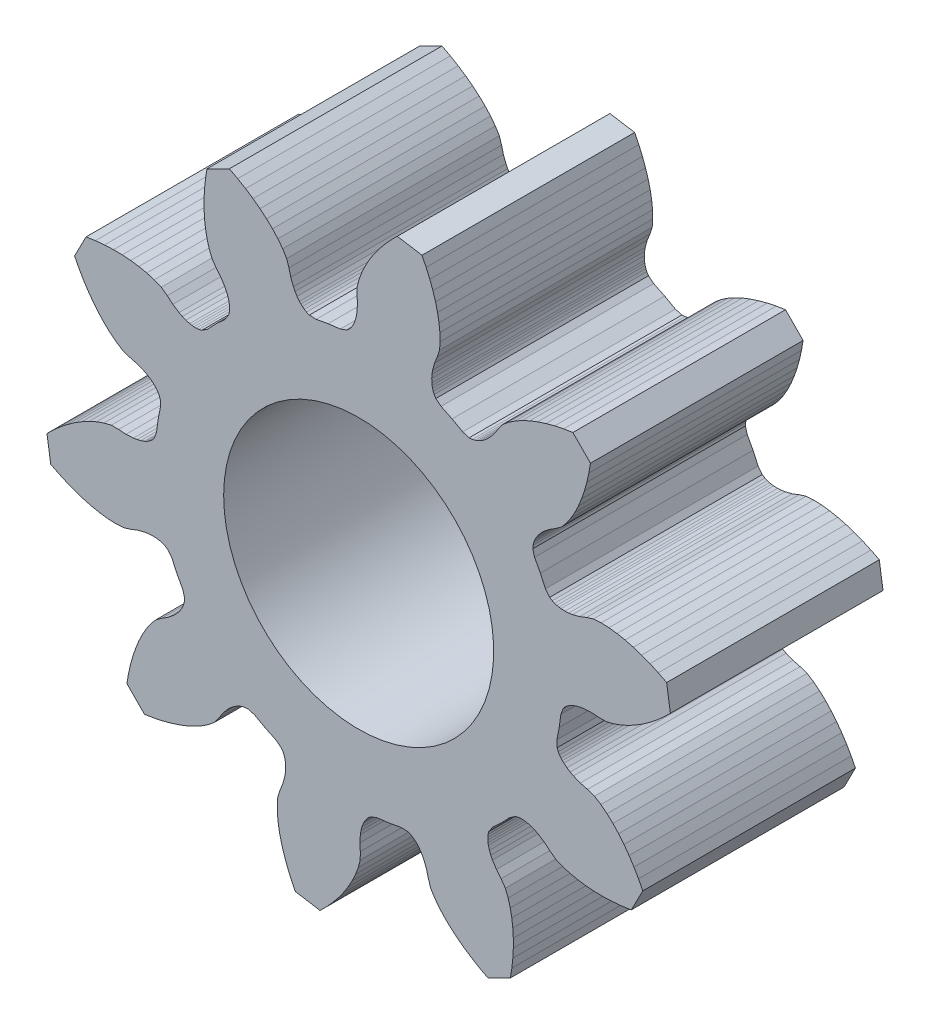
SolidWorks part; units mm, degrees
material "1060 Alloy"
ref_plane "Front Plane" through (0, 0, 0) normal (0, 0, 1) x (1, 0, 0)
ref_plane "Top Plane" through (0, 0, 0) normal (0, 1, 0) x (1, 0, 0)
ref_plane "Right Plane" through (0, 0, 0) normal (1, 0, 0) x (0, 0, -1)
sketch "Sketch1" plane through (0, 0, 0) normal (0, 0, 1) x (1, 0, 0)
  line L0 (-8.7858, -3.765) -> (-8.9815, -3.5156)
  line L1 (-8.9815, -3.5156) -> (-9.1044, -3.4371)
  line L2 (-9.1044, -3.4371) -> (-9.2148, -3.3885)
  line L3 (-9.2148, -3.3885) -> (-9.3186, -3.3562)
  line L4 (-9.3186, -3.3562) -> (-9.4181, -3.3349)
  line L5 (-9.4181, -3.3349) -> (-9.5145, -3.3217)
  line L6 (-9.5145, -3.3217) -> (-9.7003, -3.3138)
  line L7 (-9.7003, -3.3138) -> (-9.8793, -3.3247)
  line L8 (-9.8793, -3.3247) -> (-10.0533, -3.3502)
  line L9 (-10.0533, -3.3502) -> (-10.3894, -3.4364)
  line L10 (-10.3894, -3.4364) -> (-10.7128, -3.5607)
  line L11 (-10.7128, -3.5607) -> (-11.0431, -3.6644)
  line L12 (-11.0431, -3.6644) -> (-11.4, -3.6866)
  line L13 (-11.4, -3.6866) -> (-11.7679, -3.6716)
  line L14 (-11.7679, -3.6716) -> (-12.1438, -3.6256)
  line L15 (-12.1438, -3.6256) -> (-12.5259, -3.5514)
  line L16 (-12.5259, -3.5514) -> (-12.9126, -3.4504)
  line L17 (-12.9126, -3.4504) -> (-13.3028, -3.3238)
  line L18 (-13.3028, -3.3238) -> (-13.6953, -3.1723)
  line L19 (-13.6953, -3.1723) -> (-14.0889, -2.9962)
  line L20 (-14.0889, -2.9962) -> (-14.4827, -2.7961)
  line L21 (-14.4827, -2.7961) -> (-14.6595, -1.6321)
  line L22 (-14.6595, -1.6321) -> (-14.343, -1.324)
  line L23 (-14.343, -1.324) -> (-14.0194, -1.039)
  line L24 (-14.0194, -1.039) -> (-13.6897, -0.7777)
  line L25 (-13.6897, -0.7777) -> (-13.3547, -0.5409)
  line L26 (-13.3547, -0.5409) -> (-13.0154, -0.3297)
  line L27 (-13.0154, -0.3297) -> (-12.6726, -0.1453)
  line L28 (-12.6726, -0.1453) -> (-12.3273, 0.0103)
  line L29 (-12.3273, 0.0103) -> (-11.9805, 0.1339)
  line L30 (-11.9805, 0.1339) -> (-11.6331, 0.2187)
  line L31 (-11.6331, 0.2187) -> (-11.2869, 0.2178)
  line L32 (-11.2869, 0.2178) -> (-10.9412, 0.1951)
  line L33 (-10.9412, 0.1951) -> (-10.5947, 0.2127)
  line L34 (-10.5947, 0.2127) -> (-10.421, 0.24)
  line L35 (-10.421, 0.24) -> (-10.2468, 0.2828)
  line L36 (-10.2468, 0.2828) -> (-10.0717, 0.3455)
  line L37 (-10.0717, 0.3455) -> (-9.9836, 0.3867)
  line L38 (-9.9836, 0.3867) -> (-9.895, 0.4366)
  line L39 (-9.895, 0.4366) -> (-9.8054, 0.4983)
  line L40 (-9.8054, 0.4983) -> (-9.7144, 0.5775)
  line L41 (-9.7144, 0.5775) -> (-9.6204, 0.689)
  line L42 (-9.6204, 0.689) -> (-9.5076, 0.9853)
  line L43 (-9.5076, 0.9853) -> (-9.4312, 1.5547)
  line L44 (-9.4312, 1.5547) -> (-9.3208, 2.1184)
  line L45 (-9.3208, 2.1184) -> (-9.3325, 2.4352)
  line L46 (-9.3325, 2.4352) -> (-9.3858, 2.571)
  line L47 (-9.3858, 2.571) -> (-9.4466, 2.6752)
  line L48 (-9.4466, 2.6752) -> (-9.5116, 2.7624)
  line L49 (-9.5116, 2.7624) -> (-9.5796, 2.8381)
  line L50 (-9.5796, 2.8381) -> (-9.6498, 2.9054)
  line L51 (-9.6498, 2.9054) -> (-9.7955, 3.021)
  line L52 (-9.7955, 3.021) -> (-9.9467, 3.1175)
  line L53 (-9.9467, 3.1175) -> (-10.1024, 3.199)
  line L54 (-10.1024, 3.199) -> (-10.425, 3.3269)
  line L55 (-10.425, 3.3269) -> (-10.7597, 3.4164)
  line L56 (-10.7597, 3.4164) -> (-11.0878, 3.5266)
  line L57 (-11.0878, 3.5266) -> (-11.3896, 3.7184)
  line L58 (-11.3896, 3.7184) -> (-11.6785, 3.9468)
  line L59 (-11.6785, 3.9468) -> (-11.9556, 4.205)
  line L60 (-11.9556, 4.205) -> (-12.221, 4.4896)
  line L61 (-12.221, 4.4896) -> (-12.4746, 4.7986)
  line L62 (-12.4746, 4.7986) -> (-12.7159, 5.1304)
  line L63 (-12.7159, 5.1304) -> (-12.9443, 5.4837)
  line L64 (-12.9443, 5.4837) -> (-13.1593, 5.8575)
  line L65 (-13.1593, 5.8575) -> (-13.3602, 6.2508)
  line L66 (-13.3602, 6.2508) -> (-12.8191, 7.2965)
  line L67 (-12.8191, 7.2965) -> (-12.3819, 7.3597)
  line L68 (-12.3819, 7.3597) -> (-11.9526, 7.4001)
  line L69 (-11.9526, 7.4001) -> (-11.5323, 7.4176)
  line L70 (-11.5323, 7.4176) -> (-11.1221, 7.4123)
  line L71 (-11.1221, 7.4123) -> (-10.7234, 7.3838)
  line L72 (-10.7234, 7.3838) -> (-10.3377, 7.3315)
  line L73 (-10.3377, 7.3315) -> (-9.9669, 7.2544)
  line L74 (-9.9669, 7.2544) -> (-9.6137, 7.1505)
  line L75 (-9.6137, 7.1505) -> (-9.2828, 7.0149)
  line L76 (-9.2828, 7.0149) -> (-9.0033, 6.8107)
  line L77 (-9.0033, 6.8107) -> (-8.7368, 6.5892)
  line L78 (-8.7368, 6.5892) -> (-8.4462, 6.3997)
  line L79 (-8.4462, 6.3997) -> (-8.2897, 6.3197)
  line L80 (-8.2897, 6.3197) -> (-8.1236, 6.2519)
  line L81 (-8.1236, 6.2519) -> (-7.945, 6.1998)
  line L82 (-7.945, 6.1998) -> (-7.8496, 6.1813)
  line L83 (-7.8496, 6.1813) -> (-7.7485, 6.1696)
  line L84 (-7.7485, 6.1696) -> (-7.6398, 6.1668)
  line L85 (-7.6398, 6.1668) -> (-7.5196, 6.1774)
  line L86 (-7.5196, 6.1774) -> (-7.378, 6.2124)
  line L87 (-7.378, 6.2124) -> (-7.1126, 6.3858)
  line L88 (-7.1126, 6.3858) -> (-6.7162, 6.8015)
  line L89 (-6.7162, 6.8015) -> (-6.2955, 7.1927)
  line L90 (-6.2955, 7.1927) -> (-6.1188, 7.4559)
  line L91 (-6.1188, 7.4559) -> (-6.082, 7.597)
  line L92 (-6.082, 7.597) -> (-6.07, 7.7171)
  line L93 (-6.07, 7.7171) -> (-6.0713, 7.8258)
  line L94 (-6.0713, 7.8258) -> (-6.0818, 7.927)
  line L95 (-6.0818, 7.927) -> (-6.099, 8.0227)
  line L96 (-6.099, 8.0227) -> (-6.1489, 8.2019)
  line L97 (-6.1489, 8.2019) -> (-6.2146, 8.3688)
  line L98 (-6.2146, 8.3688) -> (-6.2927, 8.5263)
  line L99 (-6.2927, 8.5263) -> (-6.4784, 8.8194)
  line L100 (-6.4784, 8.8194) -> (-6.6966, 9.0885)
  line L101 (-6.6966, 9.0885) -> (-6.8973, 9.3706)
  line L102 (-6.8973, 9.3706) -> (-7.0287, 9.7032)
  line L103 (-7.0287, 9.7032) -> (-7.1282, 10.0577)
  line L104 (-7.1282, 10.0577) -> (-7.2006, 10.4294)
  line L105 (-7.2006, 10.4294) -> (-7.248, 10.8157)
  line L106 (-7.248, 10.8157) -> (-7.2715, 11.2148)
  line L107 (-7.2715, 11.2148) -> (-7.2717, 11.625)
  line L108 (-7.2717, 11.625) -> (-7.2489, 12.0451)
  line L109 (-7.2489, 12.0451) -> (-7.2031, 12.4739)
  line L110 (-7.2031, 12.4739) -> (-7.1344, 12.9102)
  line L111 (-7.1344, 12.9102) -> (-6.0821, 13.4381)
  line L112 (-6.0821, 13.4381) -> (-5.6913, 13.2322)
  line L113 (-5.6913, 13.2322) -> (-5.3202, 13.0126)
  line L114 (-5.3202, 13.0126) -> (-4.9698, 12.7797)
  line L115 (-4.9698, 12.7797) -> (-4.6411, 12.5343)
  line L116 (-4.6411, 12.5343) -> (-4.3353, 12.2769)
  line L117 (-4.3353, 12.2769) -> (-4.054, 12.0079)
  line L118 (-4.054, 12.0079) -> (-3.7993, 11.7276)
  line L119 (-3.7993, 11.7276) -> (-3.5746, 11.4359)
  line L120 (-3.5746, 11.4359) -> (-3.3866, 11.1317)
  line L121 (-3.3866, 11.1317) -> (-3.2805, 10.8022)
  line L122 (-3.2805, 10.8022) -> (-3.1952, 10.4664)
  line L123 (-3.1952, 10.4664) -> (-3.0714, 10.1422)
  line L124 (-3.0714, 10.1422) -> (-2.9918, 9.9855)
  line L125 (-2.9918, 9.9855) -> (-2.8973, 9.833)
  line L126 (-2.8973, 9.833) -> (-2.7835, 9.6859)
  line L127 (-2.7835, 9.6859) -> (-2.7171, 9.6149)
  line L128 (-2.7171, 9.6149) -> (-2.6422, 9.546)
  line L129 (-2.6422, 9.546) -> (-2.5559, 9.4799)
  line L130 (-2.5559, 9.4799) -> (-2.4524, 9.4178)
  line L131 (-2.4524, 9.4178) -> (-2.3173, 9.3628)
  line L132 (-2.3173, 9.3628) -> (-2.0007, 9.3471)
  line L133 (-2.0007, 9.3471) -> (-1.4356, 9.4504)
  line L134 (-1.4356, 9.4504) -> (-0.8654, 9.5196)
  line L135 (-0.8654, 9.5196) -> (-0.5677, 9.6287)
  line L136 (-0.5677, 9.6287) -> (-0.455, 9.7213)
  line L137 (-0.455, 9.7213) -> (-0.3747, 9.8113)
  line L138 (-0.3747, 9.8113) -> (-0.3119, 9.9001)
  line L139 (-0.3119, 9.9001) -> (-0.2608, 9.9881)
  line L140 (-0.2608, 9.9881) -> (-0.2185, 10.0757)
  line L141 (-0.2185, 10.0757) -> (-0.1536, 10.2499)
  line L142 (-0.1536, 10.2499) -> (-0.1086, 10.4236)
  line L143 (-0.1086, 10.4236) -> (-0.0792, 10.5969)
  line L144 (-0.0792, 10.5969) -> (-0.0572, 10.9432)
  line L145 (-0.0572, 10.9432) -> (-0.0755, 11.2892)
  line L146 (-0.0755, 11.2892) -> (-0.0721, 11.6353)
  line L147 (-0.0721, 11.6353) -> (0.0171, 11.9816)
  line L148 (0.0171, 11.9816) -> (0.145, 12.3269)
  line L149 (0.145, 12.3269) -> (0.3049, 12.6702)
  line L150 (0.3049, 12.6702) -> (0.4936, 13.0106)
  line L151 (0.4936, 13.0106) -> (0.7091, 13.3473)
  line L152 (0.7091, 13.3473) -> (0.9501, 13.6793)
  line L153 (0.9501, 13.6793) -> (1.2155, 14.0057)
  line L154 (1.2155, 14.0057) -> (1.5046, 14.3256)
  line L155 (1.5046, 14.3256) -> (1.8166, 14.6383)
  line L156 (1.8166, 14.6383) -> (2.9783, 14.4468)
  line L157 (2.9783, 14.4468) -> (3.1734, 14.0506)
  line L158 (3.1734, 14.0506) -> (3.3445, 13.6548)
  line L159 (3.3445, 13.6548) -> (3.4911, 13.2604)
  line L160 (3.4911, 13.2604) -> (3.6128, 12.8687)
  line L161 (3.6128, 12.8687) -> (3.7089, 12.4806)
  line L162 (3.7089, 12.4806) -> (3.7783, 12.0977)
  line L163 (3.7783, 12.0977) -> (3.8196, 11.7212)
  line L164 (3.8196, 11.7212) -> (3.83, 11.3531)
  line L165 (3.83, 11.3531) -> (3.8032, 10.9965)
  line L166 (3.8032, 10.9965) -> (3.6954, 10.6676)
  line L167 (3.6954, 10.6676) -> (3.567, 10.3458)
  line L168 (3.567, 10.3458) -> (3.4767, 10.0108)
  line L169 (3.4767, 10.0108) -> (3.4489, 9.8372)
  line L170 (3.4489, 9.8372) -> (3.4358, 9.6583)
  line L171 (3.4358, 9.6583) -> (3.4414, 9.4724)
  line L172 (3.4414, 9.4724) -> (3.4534, 9.3759)
  line L173 (3.4534, 9.3759) -> (3.4734, 9.2761)
  line L174 (3.4734, 9.2761) -> (3.5044, 9.1719)
  line L175 (3.5044, 9.1719) -> (3.5516, 9.0609)
  line L176 (3.5516, 9.0609) -> (3.6286, 8.937)
  line L177 (3.6286, 8.937) -> (3.8755, 8.7381)
  line L178 (3.8755, 8.7381) -> (4.3934, 8.4896)
  line L179 (4.3934, 8.4896) -> (4.8954, 8.2104)
  line L180 (4.8954, 8.2104) -> (5.2004, 8.1237)
  line L181 (5.2004, 8.1237) -> (5.346, 8.1323)
  line L182 (5.346, 8.1323) -> (5.4639, 8.1579)
  line L183 (5.4639, 8.1579) -> (5.5669, 8.1929)
  line L184 (5.5669, 8.1929) -> (5.6599, 8.2341)
  line L185 (5.6599, 8.2341) -> (5.7456, 8.2801)
  line L186 (5.7456, 8.2801) -> (5.9005, 8.3829)
  line L187 (5.9005, 8.3829) -> (6.039, 8.4969)
  line L188 (6.039, 8.4969) -> (6.1647, 8.6198)
  line L189 (6.1647, 8.6198) -> (6.386, 8.8871)
  line L190 (6.386, 8.8871) -> (6.5746, 9.1777)
  line L191 (6.5746, 9.1777) -> (6.7808, 9.4557)
  line L192 (6.7808, 9.4557) -> (7.0565, 9.6835)
  line L193 (7.0565, 9.6835) -> (7.3629, 9.8877)
  line L194 (7.3629, 9.8877) -> (7.6941, 10.0714)
  line L195 (7.6941, 10.0714) -> (8.0468, 10.2359)
  line L196 (8.0468, 10.2359) -> (8.4191, 10.3816)
  line L197 (8.4191, 10.3816) -> (8.8092, 10.5085)
  line L198 (8.8092, 10.5085) -> (9.2158, 10.6166)
  line L199 (9.2158, 10.6166) -> (9.6377, 10.7055)
  line L200 (9.6377, 10.7055) -> (10.0739, 10.7751)
  line L201 (10.0739, 10.7751) -> (10.9011, 9.9373)
  line L202 (10.9011, 9.9373) -> (10.8261, 9.5021)
  line L203 (10.8261, 9.5021) -> (10.7319, 9.0813)
  line L204 (10.7319, 9.0813) -> (10.6187, 8.6761)
  line L205 (10.6187, 8.6761) -> (10.4869, 8.2876)
  line L206 (10.4869, 8.2876) -> (10.3365, 7.9173)
  line L207 (10.3365, 7.9173) -> (10.1676, 7.5666)
  line L208 (10.1676, 7.5666) -> (9.9797, 7.2377)
  line L209 (9.9797, 7.2377) -> (9.7718, 6.9339)
  line L210 (9.7718, 6.9339) -> (9.5405, 6.6611)
  line L211 (9.5405, 6.6611) -> (9.26, 6.4584)
  line L212 (9.26, 6.4584) -> (8.9669, 6.2735)
  line L213 (8.9669, 6.2735) -> (8.6969, 6.0556)
  line L214 (8.6969, 6.0556) -> (8.5725, 5.9314)
  line L215 (8.5725, 5.9314) -> (8.4567, 5.7944)
  line L216 (8.4567, 5.7944) -> (8.3519, 5.6407)
  line L217 (8.3519, 5.6407) -> (8.3049, 5.5556)
  line L218 (8.3049, 5.5556) -> (8.2625, 5.4631)
  line L219 (8.2625, 5.4631) -> (8.2263, 5.3606)
  line L220 (8.2263, 5.3606) -> (8.1992, 5.243)
  line L221 (8.1992, 5.243) -> (8.1887, 5.0975)
  line L222 (8.1887, 5.0975) -> (8.2716, 4.7916)
  line L223 (8.2716, 4.7916) -> (8.5445, 4.2861)
  line L224 (8.5445, 4.2861) -> (8.7865, 3.7651)
  line L225 (8.7865, 3.7651) -> (8.9822, 3.5157)
  line L226 (8.9822, 3.5157) -> (9.1051, 3.4371)
  line L227 (9.1051, 3.4371) -> (9.2155, 3.3885)
  line L228 (9.2155, 3.3885) -> (9.3194, 3.3563)
  line L229 (9.3194, 3.3563) -> (9.4189, 3.3349)
  line L230 (9.4189, 3.3349) -> (9.5152, 3.3218)
  line L231 (9.5152, 3.3218) -> (9.701, 3.3139)
  line L232 (9.701, 3.3139) -> (9.8801, 3.3247)
  line L233 (9.8801, 3.3247) -> (10.054, 3.3503)
  line L234 (10.054, 3.3503) -> (10.3901, 3.4364)
  line L235 (10.3901, 3.4364) -> (10.7135, 3.5607)
  line L236 (10.7135, 3.5607) -> (11.0438, 3.6644)
  line L237 (11.0438, 3.6644) -> (11.4007, 3.6867)
  line L238 (11.4007, 3.6867) -> (11.7686, 3.6717)
  line L239 (11.7686, 3.6717) -> (12.1445, 3.6257)
  line L240 (12.1445, 3.6257) -> (12.5266, 3.5514)
  line L241 (12.5266, 3.5514) -> (12.9134, 3.4505)
  line L242 (12.9134, 3.4505) -> (13.3036, 3.3239)
  line L243 (13.3036, 3.3239) -> (13.696, 3.1723)
  line L244 (13.696, 3.1723) -> (14.0897, 2.9963)
  line L245 (14.0897, 2.9963) -> (14.4834, 2.7962)
  line L246 (14.4834, 2.7962) -> (14.6603, 1.6322)
  line L247 (14.6603, 1.6322) -> (14.3438, 1.3241)
  line L248 (14.3438, 1.3241) -> (14.0202, 1.0391)
  line L249 (14.0202, 1.0391) -> (13.6904, 0.7778)
  line L250 (13.6904, 0.7778) -> (13.3555, 0.541)
  line L251 (13.3555, 0.541) -> (13.0161, 0.3297)
  line L252 (13.0161, 0.3297) -> (12.6734, 0.1453)
  line L253 (12.6734, 0.1453) -> (12.3281, -0.0103)
  line L254 (12.3281, -0.0103) -> (11.9812, -0.1338)
  line L255 (11.9812, -0.1338) -> (11.6338, -0.2186)
  line L256 (11.6338, -0.2186) -> (11.2877, -0.2177)
  line L257 (11.2877, -0.2177) -> (10.9419, -0.1951)
  line L258 (10.9419, -0.1951) -> (10.5954, -0.2126)
  line L259 (10.5954, -0.2126) -> (10.4217, -0.2399)
  line L260 (10.4217, -0.2399) -> (10.2475, -0.2827)
  line L261 (10.2475, -0.2827) -> (10.0725, -0.3455)
  line L262 (10.0725, -0.3455) -> (9.9844, -0.3867)
  line L263 (9.9844, -0.3867) -> (9.8957, -0.4366)
  line L264 (9.8957, -0.4366) -> (9.8061, -0.4982)
  line L265 (9.8061, -0.4982) -> (9.7151, -0.5774)
  line L266 (9.7151, -0.5774) -> (9.6211, -0.689)
  line L267 (9.6211, -0.689) -> (9.5083, -0.9852)
  line L268 (9.5083, -0.9852) -> (9.4319, -1.5546)
  line L269 (9.4319, -1.5546) -> (9.3215, -2.1183)
  line L270 (9.3215, -2.1183) -> (9.3333, -2.4351)
  line L271 (9.3333, -2.4351) -> (9.3865, -2.5709)
  line L272 (9.3865, -2.5709) -> (9.4473, -2.6751)
  line L273 (9.4473, -2.6751) -> (9.5123, -2.7623)
  line L274 (9.5123, -2.7623) -> (9.5803, -2.838)
  line L275 (9.5803, -2.838) -> (9.6505, -2.9053)
  line L276 (9.6505, -2.9053) -> (9.7962, -3.0209)
  line L277 (9.7962, -3.0209) -> (9.9474, -3.1174)
  line L278 (9.9474, -3.1174) -> (10.1032, -3.199)
  line L279 (10.1032, -3.199) -> (10.4257, -3.3268)
  line L280 (10.4257, -3.3268) -> (10.7604, -3.4163)
  line L281 (10.7604, -3.4163) -> (11.0886, -3.5266)
  line L282 (11.0886, -3.5266) -> (11.3904, -3.7184)
  line L283 (11.3904, -3.7184) -> (11.6792, -3.9467)
  line L284 (11.6792, -3.9467) -> (11.9563, -4.2049)
  line L285 (11.9563, -4.2049) -> (12.2217, -4.4896)
  line L286 (12.2217, -4.4896) -> (12.4753, -4.7986)
  line L287 (12.4753, -4.7986) -> (12.7166, -5.1303)
  line L288 (12.7166, -5.1303) -> (12.945, -5.4836)
  line L289 (12.945, -5.4836) -> (13.16, -5.8574)
  line L290 (13.16, -5.8574) -> (13.3609, -6.2508)
  line L291 (13.3609, -6.2508) -> (12.8198, -7.2964)
  line L292 (12.8198, -7.2964) -> (12.3827, -7.3596)
  line L293 (12.3827, -7.3596) -> (11.9534, -7.4)
  line L294 (11.9534, -7.4) -> (11.533, -7.4176)
  line L295 (11.533, -7.4176) -> (11.1228, -7.4122)
  line L296 (11.1228, -7.4122) -> (10.7241, -7.3837)
  line L297 (10.7241, -7.3837) -> (10.3384, -7.3314)
  line L298 (10.3384, -7.3314) -> (9.9676, -7.2543)
  line L299 (9.9676, -7.2543) -> (9.6144, -7.1504)
  line L300 (9.6144, -7.1504) -> (9.2835, -7.0148)
  line L301 (9.2835, -7.0148) -> (9.004, -6.8106)
  line L302 (9.004, -6.8106) -> (8.7376, -6.5891)
  line L303 (8.7376, -6.5891) -> (8.4469, -6.3996)
  line L304 (8.4469, -6.3996) -> (8.2904, -6.3196)
  line L305 (8.2904, -6.3196) -> (8.1243, -6.2519)
  line L306 (8.1243, -6.2519) -> (7.9458, -6.1997)
  line L307 (7.9458, -6.1997) -> (7.8503, -6.1812)
  line L308 (7.8503, -6.1812) -> (7.7492, -6.1695)
  line L309 (7.7492, -6.1695) -> (7.6405, -6.1668)
  line L310 (7.6405, -6.1668) -> (7.5203, -6.1773)
  line L311 (7.5203, -6.1773) -> (7.3787, -6.2123)
  line L312 (7.3787, -6.2123) -> (7.1133, -6.3857)
  line L313 (7.1133, -6.3857) -> (6.7169, -6.8014)
  line L314 (6.7169, -6.8014) -> (6.2962, -7.1926)
  line L315 (6.2962, -7.1926) -> (6.1195, -7.4558)
  line L316 (6.1195, -7.4558) -> (6.0828, -7.597)
  line L317 (6.0828, -7.597) -> (6.0707, -7.717)
  line L318 (6.0707, -7.717) -> (6.0721, -7.8257)
  line L319 (6.0721, -7.8257) -> (6.0825, -7.927)
  line L320 (6.0825, -7.927) -> (6.0998, -8.0227)
  line L321 (6.0998, -8.0227) -> (6.1497, -8.2018)
  line L322 (6.1497, -8.2018) -> (6.2153, -8.3687)
  line L323 (6.2153, -8.3687) -> (6.2934, -8.5263)
  line L324 (6.2934, -8.5263) -> (6.4792, -8.8193)
  line L325 (6.4792, -8.8193) -> (6.6973, -9.0885)
  line L326 (6.6973, -9.0885) -> (6.898, -9.3705)
  line L327 (6.898, -9.3705) -> (7.0294, -9.7031)
  line L328 (7.0294, -9.7031) -> (7.1289, -10.0576)
  line L329 (7.1289, -10.0576) -> (7.2013, -10.4293)
  line L330 (7.2013, -10.4293) -> (7.2488, -10.8157)
  line L331 (7.2488, -10.8157) -> (7.2723, -11.2147)
  line L332 (7.2723, -11.2147) -> (7.2725, -11.6249)
  line L333 (7.2725, -11.6249) -> (7.2496, -12.045)
  line L334 (7.2496, -12.045) -> (7.2038, -12.4738)
  line L335 (7.2038, -12.4738) -> (7.1351, -12.9101)
  line L336 (7.1351, -12.9101) -> (6.0828, -13.438)
  line L337 (6.0828, -13.438) -> (5.692, -13.2322)
  line L338 (5.692, -13.2322) -> (5.3209, -13.0125)
  line L339 (5.3209, -13.0125) -> (4.9705, -12.7797)
  line L340 (4.9705, -12.7797) -> (4.6418, -12.5342)
  line L341 (4.6418, -12.5342) -> (4.336, -12.2768)
  line L342 (4.336, -12.2768) -> (4.0547, -12.0078)
  line L343 (4.0547, -12.0078) -> (3.8, -11.7275)
  line L344 (3.8, -11.7275) -> (3.5754, -11.4358)
  line L345 (3.5754, -11.4358) -> (3.3874, -11.1316)
  line L346 (3.3874, -11.1316) -> (3.2812, -10.8021)
  line L347 (3.2812, -10.8021) -> (3.1959, -10.4663)
  line L348 (3.1959, -10.4663) -> (3.0722, -10.1422)
  line L349 (3.0722, -10.1422) -> (2.9925, -9.9854)
  line L350 (2.9925, -9.9854) -> (2.898, -9.833)
  line L351 (2.898, -9.833) -> (2.7842, -9.6859)
  line L352 (2.7842, -9.6859) -> (2.7178, -9.6148)
  line L353 (2.7178, -9.6148) -> (2.6429, -9.5459)
  line L354 (2.6429, -9.5459) -> (2.5566, -9.4798)
  line L355 (2.5566, -9.4798) -> (2.4532, -9.4177)
  line L356 (2.4532, -9.4177) -> (2.3181, -9.3627)
  line L357 (2.3181, -9.3627) -> (2.0014, -9.347)
  line L358 (2.0014, -9.347) -> (1.4363, -9.4503)
  line L359 (1.4363, -9.4503) -> (0.8661, -9.5195)
  line L360 (0.8661, -9.5195) -> (0.5684, -9.6286)
  line L361 (0.5684, -9.6286) -> (0.4557, -9.7212)
  line L362 (0.4557, -9.7212) -> (0.3754, -9.8112)
  line L363 (0.3754, -9.8112) -> (0.3126, -9.9)
  line L364 (0.3126, -9.9) -> (0.2616, -9.988)
  line L365 (0.2616, -9.988) -> (0.2193, -10.0756)
  line L366 (0.2193, -10.0756) -> (0.1543, -10.2499)
  line L367 (0.1543, -10.2499) -> (0.1093, -10.4235)
  line L368 (0.1093, -10.4235) -> (0.0799, -10.5968)
  line L369 (0.0799, -10.5968) -> (0.058, -10.9431)
  line L370 (0.058, -10.9431) -> (0.0762, -11.2891)
  line L371 (0.0762, -11.2891) -> (0.0728, -11.6352)
  line L372 (0.0728, -11.6352) -> (-0.0163, -11.9816)
  line L373 (-0.0163, -11.9816) -> (-0.1442, -12.3268)
  line L374 (-0.1442, -12.3268) -> (-0.3042, -12.6701)
  line L375 (-0.3042, -12.6701) -> (-0.4929, -13.0106)
  line L376 (-0.4929, -13.0106) -> (-0.7084, -13.3472)
  line L377 (-0.7084, -13.3472) -> (-0.9494, -13.6792)
  line L378 (-0.9494, -13.6792) -> (-1.2148, -14.0056)
  line L379 (-1.2148, -14.0056) -> (-1.5038, -14.3256)
  line L380 (-1.5038, -14.3256) -> (-1.8159, -14.6382)
  line L381 (-1.8159, -14.6382) -> (-2.9775, -14.4467)
  line L382 (-2.9775, -14.4467) -> (-3.1727, -14.0505)
  line L383 (-3.1727, -14.0505) -> (-3.3438, -13.6547)
  line L384 (-3.3438, -13.6547) -> (-3.4904, -13.2603)
  line L385 (-3.4904, -13.2603) -> (-3.6121, -12.8686)
  line L386 (-3.6121, -12.8686) -> (-3.7081, -12.4806)
  line L387 (-3.7081, -12.4806) -> (-3.7776, -12.0976)
  line L388 (-3.7776, -12.0976) -> (-3.8189, -11.7211)
  line L389 (-3.8189, -11.7211) -> (-3.8292, -11.3531)
  line L390 (-3.8292, -11.3531) -> (-3.8025, -10.9965)
  line L391 (-3.8025, -10.9965) -> (-3.6947, -10.6675)
  line L392 (-3.6947, -10.6675) -> (-3.5663, -10.3457)
  line L393 (-3.5663, -10.3457) -> (-3.4759, -10.0107)
  line L394 (-3.4759, -10.0107) -> (-3.4482, -9.8371)
  line L395 (-3.4482, -9.8371) -> (-3.4351, -9.6582)
  line L396 (-3.4351, -9.6582) -> (-3.4407, -9.4723)
  line L397 (-3.4407, -9.4723) -> (-3.4526, -9.3758)
  line L398 (-3.4526, -9.3758) -> (-3.4727, -9.2761)
  line L399 (-3.4727, -9.2761) -> (-3.5037, -9.1718)
  line L400 (-3.5037, -9.1718) -> (-3.5509, -9.0608)
  line L401 (-3.5509, -9.0608) -> (-3.6279, -8.9369)
  line L402 (-3.6279, -8.9369) -> (-3.8748, -8.7381)
  line L403 (-3.8748, -8.7381) -> (-4.3927, -8.4895)
  line L404 (-4.3927, -8.4895) -> (-4.8947, -8.2103)
  line L405 (-4.8947, -8.2103) -> (-5.1996, -8.1236)
  line L406 (-5.1996, -8.1236) -> (-5.3452, -8.1323)
  line L407 (-5.3452, -8.1323) -> (-5.4632, -8.1579)
  line L408 (-5.4632, -8.1579) -> (-5.5661, -8.1928)
  line L409 (-5.5661, -8.1928) -> (-5.6592, -8.234)
  line L410 (-5.6592, -8.234) -> (-5.7448, -8.28)
  line L411 (-5.7448, -8.28) -> (-5.8998, -8.3828)
  line L412 (-5.8998, -8.3828) -> (-6.0383, -8.4968)
  line L413 (-6.0383, -8.4968) -> (-6.164, -8.6198)
  line L414 (-6.164, -8.6198) -> (-6.3852, -8.887)
  line L415 (-6.3852, -8.887) -> (-6.5738, -9.1777)
  line L416 (-6.5738, -9.1777) -> (-6.7801, -9.4557)
  line L417 (-6.7801, -9.4557) -> (-7.0558, -9.6835)
  line L418 (-7.0558, -9.6835) -> (-7.3622, -9.8876)
  line L419 (-7.3622, -9.8876) -> (-7.6933, -10.0713)
  line L420 (-7.6933, -10.0713) -> (-8.0461, -10.2358)
  line L421 (-8.0461, -10.2358) -> (-8.4183, -10.3815)
  line L422 (-8.4183, -10.3815) -> (-8.8084, -10.5085)
  line L423 (-8.8084, -10.5085) -> (-9.215, -10.6165)
  line L424 (-9.215, -10.6165) -> (-9.637, -10.7055)
  line L425 (-9.637, -10.7055) -> (-10.0731, -10.775)
  line L426 (-10.0731, -10.775) -> (-10.9004, -9.9373)
  line L427 (-10.9004, -9.9373) -> (-10.8254, -9.502)
  line L428 (-10.8254, -9.502) -> (-10.7312, -9.0812)
  line L429 (-10.7312, -9.0812) -> (-10.618, -8.676)
  line L430 (-10.618, -8.676) -> (-10.4862, -8.2876)
  line L431 (-10.4862, -8.2876) -> (-10.3358, -7.9172)
  line L432 (-10.3358, -7.9172) -> (-10.1669, -7.5665)
  line L433 (-10.1669, -7.5665) -> (-9.979, -7.2377)
  line L434 (-9.979, -7.2377) -> (-9.771, -6.9339)
  line L435 (-9.771, -6.9339) -> (-9.5398, -6.661)
  line L436 (-9.5398, -6.661) -> (-9.2592, -6.4583)
  line L437 (-9.2592, -6.4583) -> (-8.9662, -6.2734)
  line L438 (-8.9662, -6.2734) -> (-8.6962, -6.0555)
  line L439 (-8.6962, -6.0555) -> (-8.5717, -5.9314)
  line L440 (-8.5717, -5.9314) -> (-8.456, -5.7943)
  line L441 (-8.456, -5.7943) -> (-8.3512, -5.6407)
  line L442 (-8.3512, -5.6407) -> (-8.3041, -5.5556)
  line L443 (-8.3041, -5.5556) -> (-8.2618, -5.4631)
  line L444 (-8.2618, -5.4631) -> (-8.2256, -5.3605)
  line L445 (-8.2256, -5.3605) -> (-8.1985, -5.243)
  line L446 (-8.1985, -5.243) -> (-8.188, -5.0975)
  line L447 (-8.188, -5.0975) -> (-8.2708, -4.7915)
  line L448 (-8.2708, -4.7915) -> (-8.5437, -4.286)
  line L449 (-8.5437, -4.286) -> (-8.7858, -3.765)
extrude "Extrude gear face" add sketch "Sketch1" along normal blind 10
sketch "Sketch3" plane through (0, 0, 0) normal (0, 0, -1) x (-1, 0, 0)
  circle A0 centre (0, 0) radius 6.35
  dimension "D1" = 12.7
extrude "Cut-Extrude1" cut sketch "Sketch3" against normal through all
